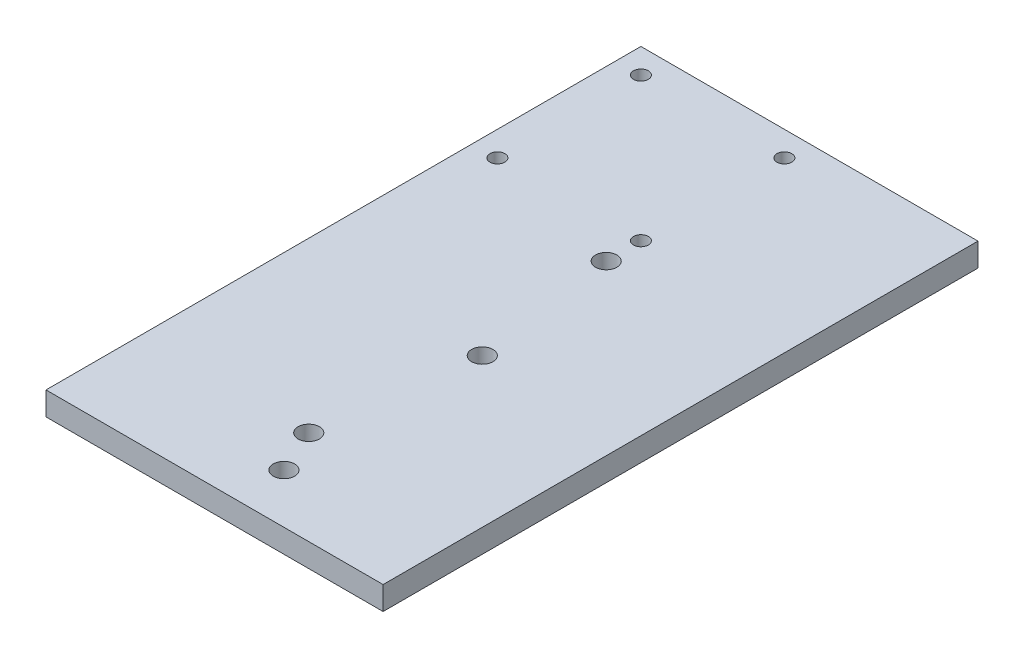
SolidWorks part; units mm, degrees
ref_plane "Front Plane" through (0, 0, 0) normal (0, 0, 1) x (1, 0, 0)
ref_plane "Top Plane" through (0, 0, 0) normal (0, 1, 0) x (1, 0, 0)
ref_plane "Right Plane" through (0, 0, 0) normal (1, 0, 0) x (0, 0, -1)
sketch "Sketch2" plane through (0, 0, 0) normal (0, 1, 0) x (1, 0, 0)
  line L2 (0, 0) -> (0, 152.4)
  line L4 (88.9, 0) -> (88.9, 152.4)
  line L10 (-1000, 76.2) -> (49000, 76.2) construction
  line L13 (0, 152.4) -> (88.9, 152.4)
  line L14 (0, 0) -> (88.9, 0)
  point P11 (0, 76.2)
  dimension "D1" = 152.4
  dimension "D2" = 88.9
extrude "Boss-Extrude1" add sketch "Sketch2" along normal blind 5.9944 contours L4 L13 L2 L14
sketch "Sketch4" plane through (0, 5.9944, 0) normal (0, 1, 0) x (1, 0, 0)
  line L0 (0, 0) -> (0, 152.4) construction
  line L1 (0, 0) -> (88.9, 0) construction
  line L2 (45.72, 100.33) -> (45.72, 24.13) construction
  circle A0 centre (45.72, 100.33) radius 2.7305
  circle A1 centre (45.72, 24.13) radius 2.7305
  point P4 (45.72, 62.23)
  dimension "D3" = 5.461
  dimension "D4" = 5.461
  dimension "D1" = 76.2
  dimension "D2" = 45.72
  dimension "D5" = 62.23
extrude "Cut-Extrude2" cut sketch "Sketch4" against normal through all both
sketch "Sketch5" plane through (0, 5.9944, 0) normal (0, 1, 0) x (1, 0, 0)
  line L0 (88.9, 0) -> (88.9, 152.4) construction
  line L5 (0, 0) -> (88.9, 0) construction
  circle A0 centre (50.8, 63.5) radius 2.7305
  circle A1 centre (50.8, 12.7) radius 2.7305
  dimension "D1" = 5.461
  dimension "D2" = 5.461
  dimension "D3" = 50.8
  dimension "D6" = 38.1
  dimension "D7" = 12.7
extrude "Cut-Extrude3" cut sketch "Sketch5" against normal through all both and the other way through all
sketch "Sketch6" plane through (0, 5.9944, 0) normal (0, 1, 0) x (1, 0, 0)
  line L0 (0, 152.4) -> (88.9, 152.4) construction
  line L1 (45.6438, 146.05) -> (8.89, 146.05) construction
  line L2 (45.6438, 146.05) -> (45.6438, 109.2962) construction
  line L3 (45.6438, 109.2962) -> (8.89, 109.2962) construction
  line L4 (8.89, 146.05) -> (8.89, 109.2962) construction
  line L5 (0, 0) -> (0, 152.4) construction
  circle A0 centre (45.6438, 109.2962) radius 1.905
  circle A1 centre (8.89, 109.2962) radius 1.905
  circle A2 centre (8.89, 146.05) radius 1.905
  circle A3 centre (45.6438, 146.05) radius 1.905
  dimension "D3" = 3.81
  dimension "D4" = 3.81
  dimension "D5" = 3.81
  dimension "D6" = 3.81
  dimension "D7" = 6.35
  dimension "D1" = 36.7538
  dimension "D2" = 36.7538
  dimension "D8" = 8.89
extrude "Cut-Extrude4" cut sketch "Sketch6" against normal through all both and the other way through all
sketch "Sketch7" plane through (0, 5.9944, 0) normal (0, 1, 0) x (1, 0, 0)
  line L0 (0, 0) -> (88.9, 0) construction
  line L1 (0, 152.4) -> (2.54, 152.4)
  line L2 (0, 152.4) -> (0, 0)
  line L3 (0, 0) -> (2.54, 0)
  line L4 (2.54, 152.4) -> (2.54, 0)
  dimension "D1" = 2.54
extrude "Cut-Extrude5" cut sketch "Sketch7" against normal through all both and the other way through all
equation "\"threaded_insert_hole\"=0.1472"
equation "\"th\"=1.25249"
